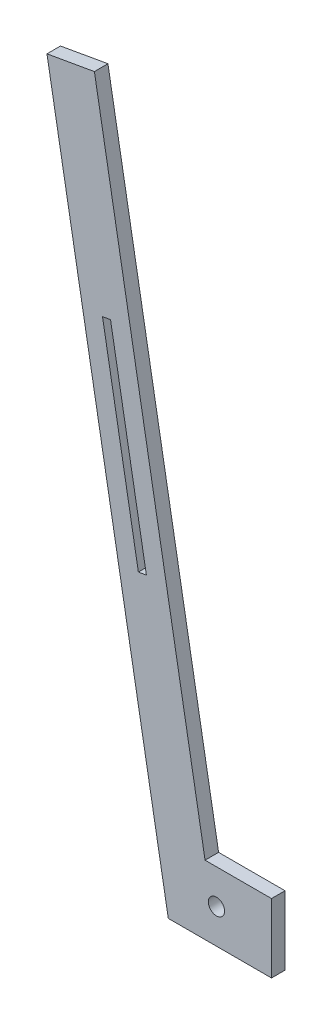
SolidWorks part; units mm, degrees
ref_plane "Front Plane" through (0, 0, 0) normal (0, 0, 1) x (1, 0, 0)
ref_plane "Top Plane" through (0, 0, 0) normal (0, 1, 0) x (1, 0, 0)
ref_plane "Right Plane" through (0, 0, 0) normal (1, 0, 0) x (0, 0, -1)
sketch "Sketch1" plane through (0, 0, 0) normal (0, 0, 1) x (1, 0, 0)
  line L0 (0, 0) -> (20.32, 0) construction
  line L1 (20.32, 12.7) -> (20.32, -12.7)
  line L2 (20.32, -12.7) -> (-17.78, -12.7)
  line L3 (-17.78, -12.7) -> (-62.5671, 241.3)
  line L4 (-62.5671, 241.3) -> (-37.5529, 245.7107)
  line L5 (-37.5529, 245.7107) -> (3.5331, 12.7)
  line L6 (20.32, 12.7) -> (3.5331, 12.7)
  circle A0 centre (0, 0) radius 3
  point P6 (20.32, 0)
  dimension "D2" = 20.32
  dimension "D3" = 25.4
  dimension "D1" = 6
  dimension "D4" = 38.1
  dimension "D5" = 25.4
  dimension "D6" = 100
  dimension "D7" = 254
extrude "Boss-Extrude1" add sketch "Sketch1" along normal mid plane 5
sketch "Sketch2" plane through (0, 0, 2.5) normal (0, 0, 1) x (1, 0, 0)
  line L0 (-37.5529, 245.7107) -> (3.5331, 12.7)
  line L1 (3.5331, 12.7) -> (-4.2044, 12.7)
  line L2 (-4.2044, 12.7) -> (-45.0572, 244.3875)
  line L3 (-37.5529, 245.7107) -> (-62.5671, 241.3) construction
  line L4 (-45.0572, 244.3875) -> (-37.5529, 245.7107)
  dimension "D1" = 7.62
extrude "Cut-Extrude1" cut sketch "Sketch2" against normal through all
sketch "Sketch3" plane through (0, 0, 0) normal (0, 0, 1) x (1, 0, 0)
  line L0 (-62.5671, 241.3) -> (-17.78, -12.7) construction
  line L1 (-42.0573, 167.5409) -> (-39.1029, 168.0619)
  line L2 (-42.0573, 167.5409) -> (-28.8253, 92.4986)
  line L3 (-28.8253, 92.4986) -> (-25.8709, 93.0195)
  line L4 (-39.1029, 168.0619) -> (-25.8709, 93.0195)
  line L5 (-45.0572, 244.3875) -> (-62.5671, 241.3) construction
  line L6 (-53.8121, 242.8437) -> (-8.7529, -12.7) construction
  line L7 (-17.78, -12.7) -> (20.32, -12.7) construction
  line L8 (-40.5801, 167.8014) -> (-27.3481, 92.759) construction
  dimension "D1" = 3
  dimension "D2" = 76.2
  dimension "D3" = 76.2
extrude "Cut-Extrude2" cut sketch "Sketch3" against normal mid plane 50.8
